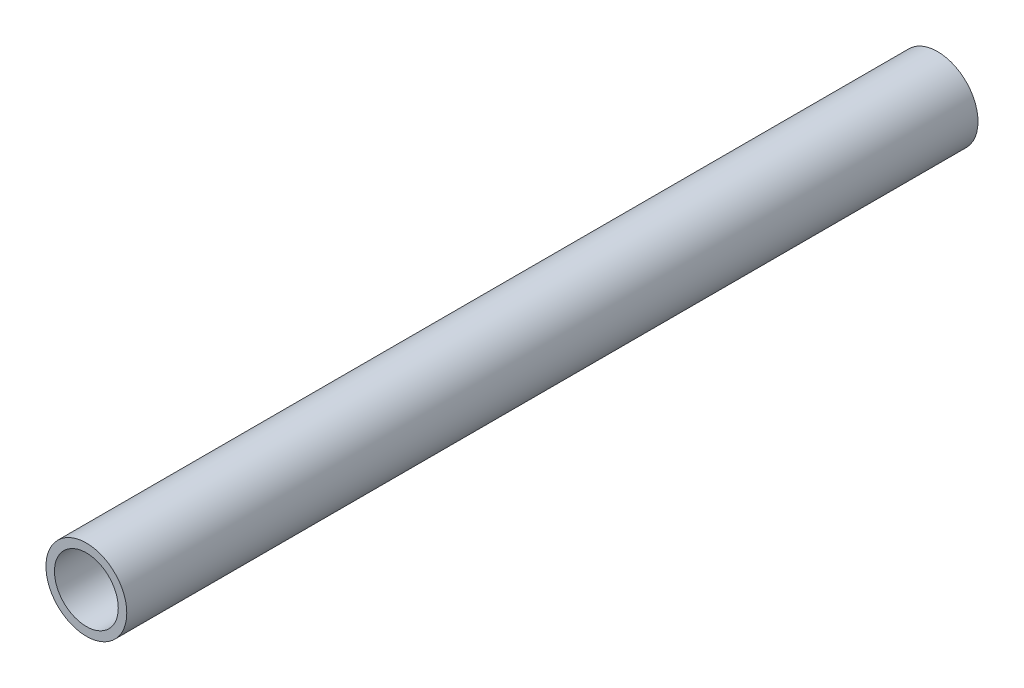
SolidWorks part; units mm, degrees
ref_plane "前基準面" through (0, 0, 0) normal (0, 0, 1) x (1, 0, 0)
ref_plane "上基準面" through (0, 0, 0) normal (0, 1, 0) x (1, 0, 0)
ref_plane "右基準面" through (0, 0, 0) normal (1, 0, 0) x (0, 0, -1)
sketch "草圖1" plane through (0, 0, 0) normal (0, 0, 1) x (1, 0, 0)
  circle A0 centre (0, 0) radius 9.5
  circle A1 centre (0, 0) radius 7.5
  dimension "D1" = 19
  dimension "D2" = 2
extrude "填料-伸長1" add sketch "草圖1" along normal blind 200
